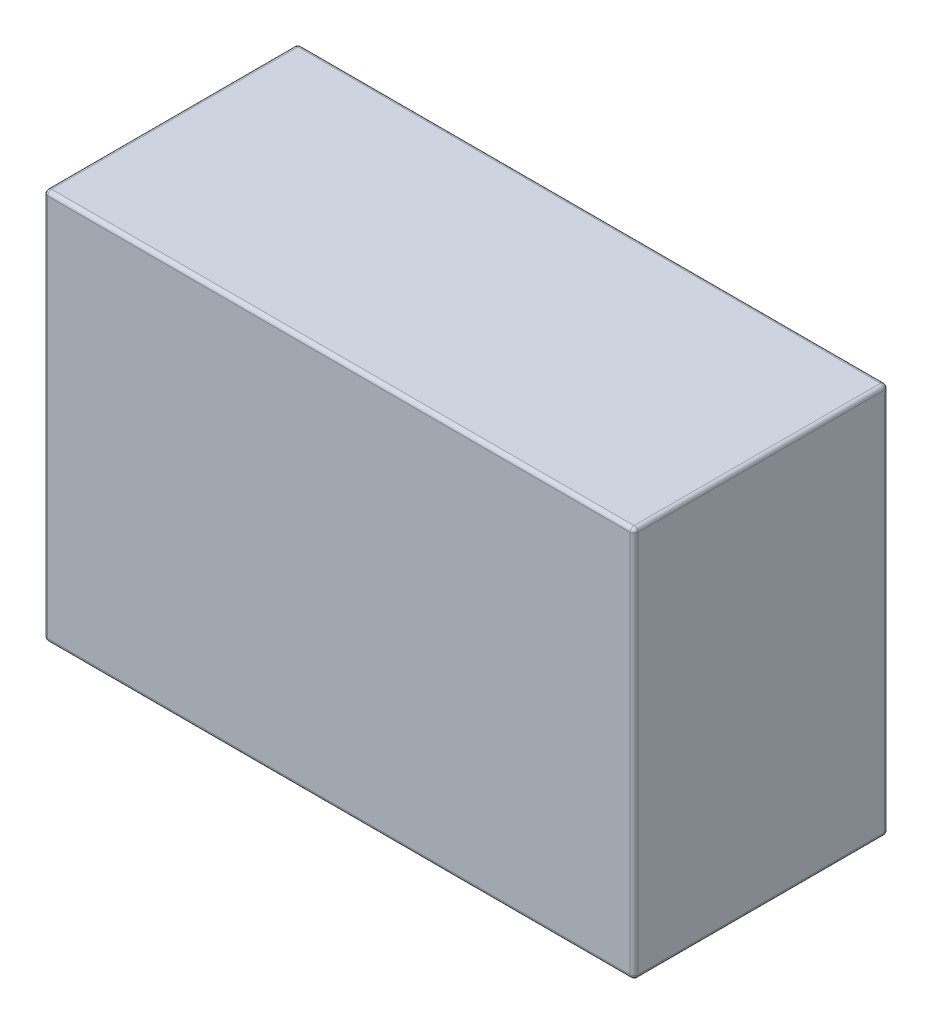
SolidWorks part; units mm, degrees
ref_plane "Front Plane" through (0, 0, 0) normal (0, 0, 1) x (1, 0, 0)
ref_plane "Top Plane" through (0, 0, 0) normal (0, 1, 0) x (1, 0, 0)
ref_plane "Right Plane" through (0, 0, 0) normal (1, 0, 0) x (0, 0, -1)
sketch "Sketch1" plane through (0, 0, 0) normal (0, 1, 0) x (1, 0, 0)
  line L1 (-75.5, -32.5) -> (75.5, -32.5)
  line L2 (-75.5, -32.5) -> (-75.5, 32.5)
  line L3 (-75.5, 32.5) -> (75.5, 32.5)
  line L4 (75.5, -32.5) -> (75.5, 32.5)
  line L5 (-75.5, -32.5) -> (75.5, 32.5) construction
  line L6 (-75.5, 32.5) -> (75.5, -32.5) construction
  point P0 (0, 0)
  dimension "D1" = 151
  dimension "D2" = 65
extrude "Boss-Extrude1" add sketch "Sketch1" along normal blind 100
fillet "Fillet1" radius 1 12 edges at (0, 0, -32.5) (75.5, 50, -32.5) (75.5, 0, 0) (0, 100, -32.5) (75.5, 100, 0) (0, 100, 32.5) (75.5, 50, 32.5) (0, 0, 32.5) (-75.5, 50, -32.5) (-75.5, 100, 0) (-75.5, 50, 32.5) (-75.5, 0, 0)
